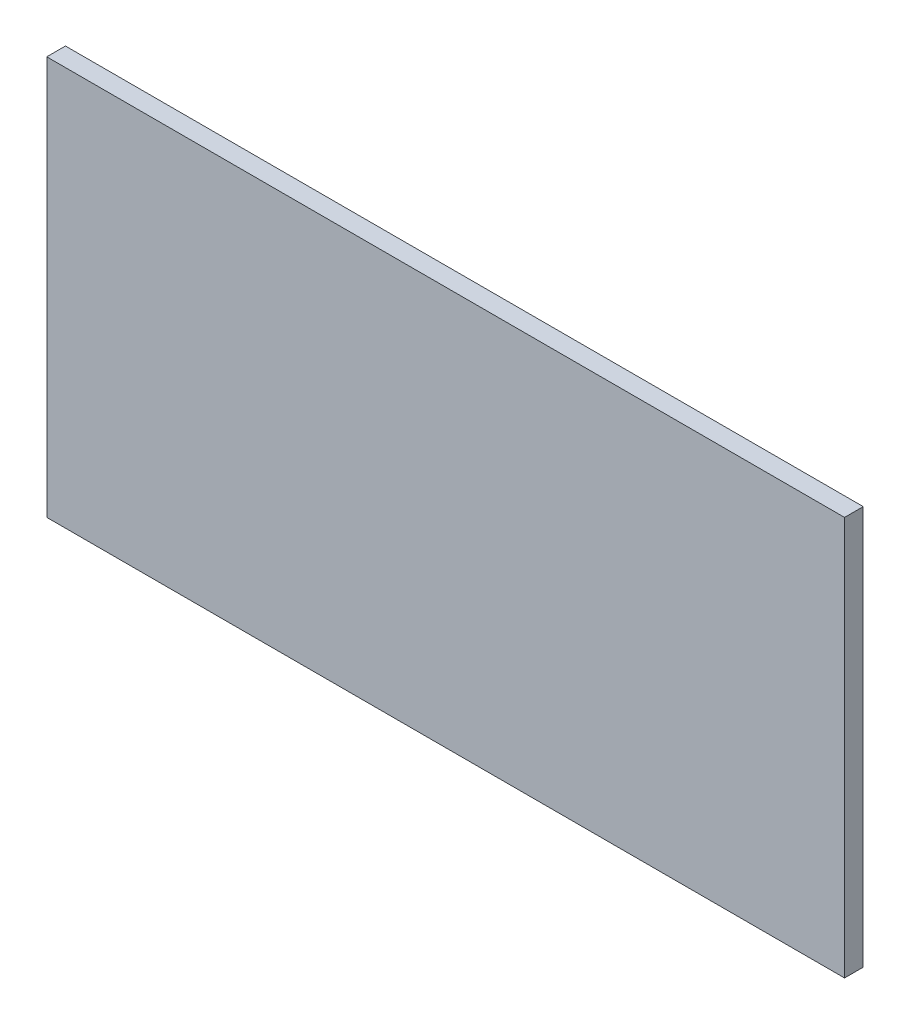
SolidWorks part; units mm, degrees
ref_plane "前视基准面" through (0, 0, 0) normal (0, 0, 1) x (1, 0, 0)
ref_plane "上视基准面" through (0, 0, 0) normal (0, 1, 0) x (1, 0, 0)
ref_plane "右视基准面" through (0, 0, 0) normal (1, 0, 0) x (0, 0, -1)
sketch "草图1" plane through (0, 0, 0) normal (0, 0, 1) x (1, 0, 0)
  line L1 (-64, 32) -> (64, 32)
  line L2 (-64, 32) -> (-64, -32)
  line L3 (-64, -32) -> (64, -32)
  line L4 (64, 32) -> (64, -32)
  line L5 (-64, 32) -> (64, -32) construction
  line L6 (-64, -32) -> (64, 32) construction
  point P0 (0, 0)
  dimension "D1" = 64
  dimension "D2" = 128
extrude "凸台-拉伸1" add sketch "草图1" along normal blind 3
